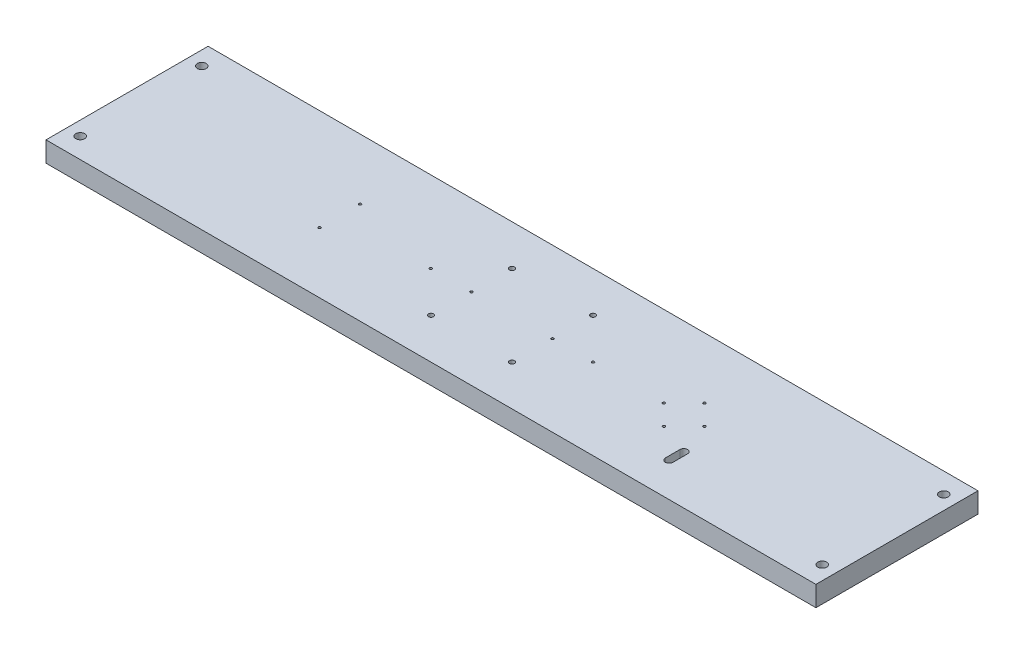
SolidWorks part; units mm, degrees
ref_plane "Front Plane" through (0, 0, 0) normal (0, 0, 1) x (1, 0, 0)
ref_plane "Top Plane" through (0, 0, 0) normal (0, 1, 0) x (1, 0, 0)
ref_plane "Right Plane" through (0, 0, 0) normal (1, 0, 0) x (0, 0, -1)
sketch "Sketch1" plane through (0, 0, 0) normal (0, 1, 0) x (1, 0, 0)
  line L1 (-241.3, -50.8) -> (241.3, -50.8)
  line L2 (-241.3, -50.8) -> (-241.3, 50.8)
  line L3 (-241.3, 50.8) -> (241.3, 50.8)
  line L4 (241.3, -50.8) -> (241.3, 50.8)
  line L5 (-241.3, -50.8) -> (241.3, 50.8) construction
  line L6 (-241.3, 50.8) -> (241.3, -50.8) construction
  point P0 (0, 0)
  dimension "D1" = 101.6
  dimension "D2" = 482.6
extrude "Boss-Extrude1" add sketch "Sketch1" along normal blind 12.7
sketch "Sketch2" plane through (0, 12.7, 0) normal (0, 1, 0) x (1, 0, 0)
  line L0 (0, 50.8) -> (0, -50.8) construction
  line L1 (241.3, 50.8) -> (-241.3, 50.8) construction
  line L2 (-241.3, -50.8) -> (241.3, -50.8) construction
  circle A0 centre (-232.5624, 38.1) radius 2.7813
  circle A1 centre (-232.5624, -38.1) radius 2.7813
  circle A2 centre (232.5624, 38.1) radius 2.7813
  circle A3 centre (232.5624, -38.1) radius 2.7813
  point P14 (0, 0)
  point P15 (0, 0)
  point P16 (0, 0)
  point P17 (0, 0)
  point P18 (0, 0)
  dimension "D1" = 465.1248
  dimension "D2" = 5.5626
  dimension "D3" = 5.5626
  dimension "D4" = 5.5626
  dimension "D5" = 5.5626
  dimension "D6" = 76.2
  dimension "D7" = 12.7
extrude "Cut-Extrude1" cut sketch "Sketch2" against normal through all
sketch "Sketch3" plane through (0, 12.7, 0) normal (0, 1, 0) x (1, 0, 0)
  line L1 (-25.4, -25.4) -> (25.4, -25.4) construction
  line L2 (-25.4, -25.4) -> (-25.4, 25.4) construction
  line L3 (-25.4, 25.4) -> (25.4, 25.4) construction
  line L4 (25.4, -25.4) -> (25.4, 25.4) construction
  line L5 (-25.4, -25.4) -> (25.4, 25.4) construction
  line L6 (-25.4, 25.4) -> (25.4, -25.4) construction
  circle A0 centre (-25.4, 25.4) radius 1.5875
  circle A1 centre (25.4, 25.4) radius 1.5875
  circle A2 centre (25.4, -25.4) radius 1.5875
  circle A3 centre (-25.4, -25.4) radius 1.5875
  point P0 (0, 0)
  dimension "D3" = 3.175
  dimension "D4" = 3.175
  dimension "D5" = 3.175
  dimension "D6" = 3.175
  dimension "D1" = 50.8
  dimension "D2" = 50.8
extrude "Cut-Extrude2" cut sketch "Sketch3" against normal through all
sketch "Sketch4" plane through (0, 12.7, 0) normal (0, 1, 0) x (1, 0, 0)
  line L0 (-241.3, 0) -> (241.3, 0) construction
  line L1 (-241.3, 50.8) -> (-241.3, -50.8) construction
  line L2 (241.3, -50.8) -> (241.3, 50.8) construction
  line L3 (0, 50.8) -> (0, -50.8) construction
  line L4 (241.3, 50.8) -> (-241.3, 50.8) construction
  line L5 (-241.3, -50.8) -> (241.3, -50.8) construction
  line L7 (-107.95, -12.7) -> (107.95, -12.7) construction
  line L8 (-107.95, -12.7) -> (-107.95, 12.7) construction
  line L9 (-107.95, 12.7) -> (107.95, 12.7) construction
  line L10 (107.95, -12.7) -> (107.95, 12.7) construction
  line L11 (-107.95, -12.7) -> (107.95, 12.7) construction
  line L12 (-107.95, 12.7) -> (107.95, -12.7) construction
  circle A0 centre (-25.4, 0) radius 0.7937
  circle A1 centre (25.4, 0) radius 0.7937
  circle A2 centre (-50.8, 0) radius 0.7937
  circle A3 centre (50.8, 0) radius 0.7937
  circle A4 centre (-107.95, 12.7) radius 0.7937
  circle A5 centre (-107.95, -12.7) radius 0.7937
  circle A6 centre (107.95, -12.7) radius 0.7937
  circle A7 centre (107.95, 12.7) radius 0.7937
  point P20 (0, 0)
  dimension "D1" = 1.5875
  dimension "D3" = 1.5875
  dimension "D5" = 1.5875
  dimension "D6" = 1.5875
  dimension "D11" = 1.5875
  dimension "D12" = 1.5875
  dimension "D13" = 1.5875
  dimension "D14" = 1.5875
  dimension "D2" = 25.4
  dimension "D4" = 25.4
  dimension "D7" = 25.4
  dimension "D8" = 25.4
  dimension "D9" = 25.4
  dimension "D10" = 215.9
extrude "Cut-Extrude3" cut sketch "Sketch4" against normal through all
sketch "Sketch5" plane through (0, 12.7, 0) normal (0, 1, 0) x (1, 0, 0)
  circle A0 centre (95.25, 0) radius 0.7937
  circle A1 centre (120.65, 0) radius 0.7937
  circle A2 centre (107.95, 12.7) radius 0.7937 construction
  point P7 (0, 0)
  point P8 (0, 0)
  point P9 (0, 0)
  dimension "D2" = 1.5875
  dimension "D4" = 1.5875
  dimension "D1" = 25.4
  dimension "D3" = 12.7
extrude "Cut-Extrude4" cut sketch "Sketch5" against normal through all
sketch "Sketch6" plane through (0, 12.7, 0) normal (0, 1, 0) x (1, 0, 0)
  line L0 (125.4899, -20.1549) -> (125.4899, -29.3751)
  line L1 (130.2397, -20.1549) -> (130.2397, -29.3751)
  line L2 (-241.3, -50.8) -> (241.3, -50.8) construction
  arc A0 (125.4899, -20.1549) -> (130.2397, -20.1549) centre (127.8648, -20.1549) cw
  arc A1 (130.2397, -29.3751) -> (125.4899, -29.3751) centre (127.8648, -29.3751) cw
  point P6 (0, 0)
  point P7 (129.6284, -41.3708)
  point P8 (129.9115, -42.3817)
  point P9 (130.2397, -20.398)
  point P10 (127.8648, -17.78)
  point P11 (127.8648, -31.75)
  dimension "D2" = 13.97
  dimension "D1" = 4.7498
  dimension "D3" = 19.05
extrude "Cut-Extrude5" cut sketch "Sketch6" against normal through all
